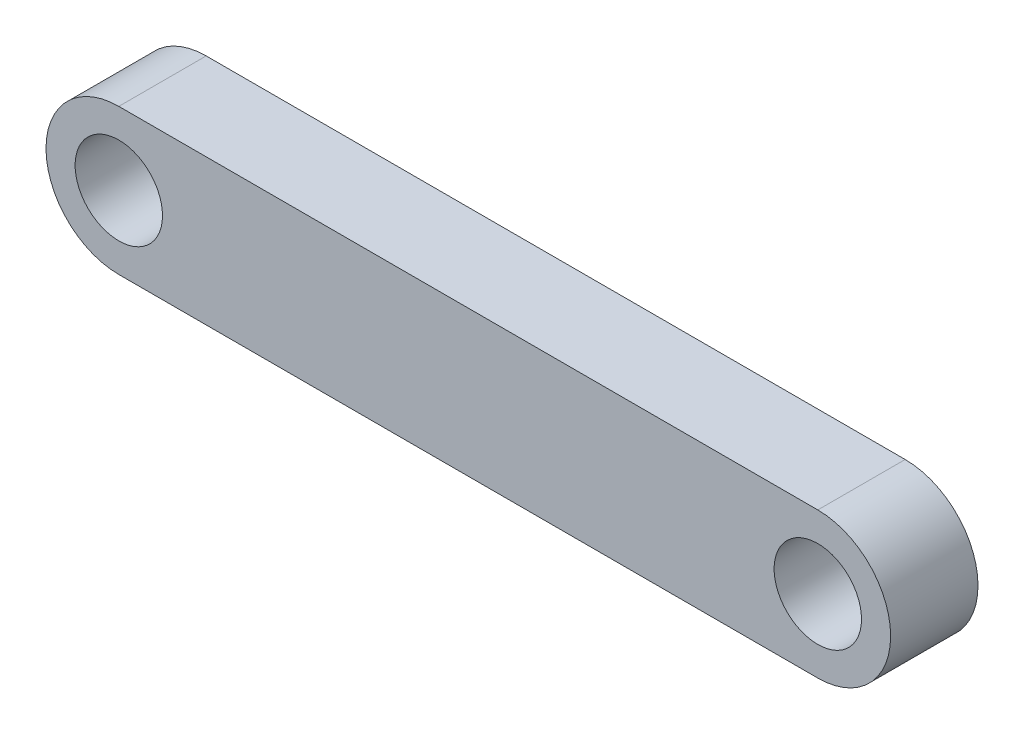
SolidWorks part; units mm, degrees
material "AISI 304"
ref_plane "Front Plane" through (0, 0, 0) normal (0, 0, 1) x (1, 0, 0)
ref_plane "Top Plane" through (0, 0, 0) normal (0, 1, 0) x (1, 0, 0)
ref_plane "Right Plane" through (0, 0, 0) normal (1, 0, 0) x (0, 0, -1)
sketch "Sketch1" plane through (0, 0, 0) normal (0, 0, 1) x (1, 0, 0)
  line L0 (0, 0) -> (48, 0)
  line L1 (0, 5) -> (48, 5)
  line L2 (0, -5) -> (48, -5)
  circle A0 centre (0, 0) radius 3
  circle A1 centre (48, 0) radius 3
  circle A2 centre (0, 0) radius 5
  circle A3 centre (48, 0) radius 5
  dimension "D1" = 48
extrude "Boss-Extrude1" add sketch "Sketch1" along normal blind 6
